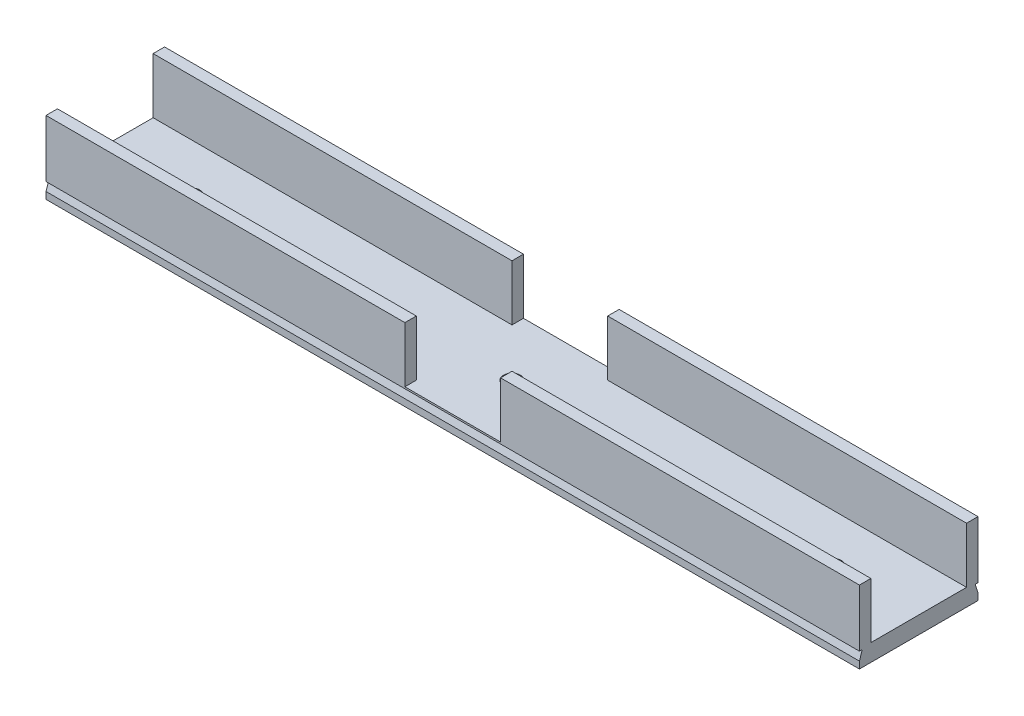
SolidWorks part; units mm, degrees
ref_plane "Front Plane" through (0, 0, 0) normal (0, 0, 1) x (1, 0, 0)
ref_plane "Top Plane" through (0, 0, 0) normal (0, 1, 0) x (1, 0, 0)
ref_plane "Right Plane" through (0, 0, 0) normal (1, 0, 0) x (0, 0, -1)
sketch "Croquis1" plane through (0, 0, 0) normal (0, 1, 0) x (1, 0, 0)
  line L0 (-71, -12.5) -> (-71, 12.5)
  line L1 (-71, -12.5) -> (71, -12.5)
  line L2 (-71, 12.5) -> (71, 12.5)
  line L3 (71, -12.5) -> (71, 12.5)
  line L4 (-71, -12.5) -> (71, 12.5) construction
  line L5 (-71, 12.5) -> (71, -12.5) construction
  line L6 (71, -10.35) -> (71, 10.35)
  line L7 (71, -10.35) -> (-71, -10.35)
  line L8 (71, 10.35) -> (-71, 10.35)
  line L9 (-71, -10.35) -> (-71, 10.35)
  line L10 (71, -10.35) -> (-71, 10.35) construction
  line L11 (71, 10.35) -> (-71, -10.35) construction
  point P1 (0, 0)
  point P2 (0, 0)
  dimension "D1" = 142
  dimension "D2" = 25
  dimension "D3" = 142
  dimension "D4" = 2.15
extrude "Saliente-Extruir2" add sketch "Croquis1" along normal blind 3 contours L3 L8 L0 L7
sketch "Croquis6" plane through (0, 3, 0) normal (0, 1, 0) x (1, 0, 0)
  line L0 (0, 0) -> (0, 6.8298) construction
  line L1 (-71, -10.35) -> (-71, 10.35) construction
  circle A0 centre (-56, 0) radius 1.5
  circle A1 centre (0, 0) radius 1.5
  circle A2 centre (56, 0) radius 1.5
  point P9 (-71, 0)
  dimension "D1" = 3
  dimension "D2" = 3
  dimension "D3" = 15
extrude "Cortar-Extruir4" cut sketch "Croquis6" against normal blind 3
sketch "Croquis7" plane through (0, 3, 0) normal (0, 1, 0) x (1, 0, 0)
  line L0 (-71, 8.35) -> (-71, 10.35)
  line L1 (-71, -10.35) -> (-71, 10.35) construction
  line L2 (-71, 10.35) -> (71, 10.35)
  line L3 (71, -10.35) -> (71, 10.35) construction
  line L4 (71, 10.35) -> (-71, 10.35) construction
  line L5 (71, 10.35) -> (71, 8.35)
  line L6 (71, 8.35) -> (-71, 8.35)
  line L7 (0, 0) -> (-103.6833, 0) construction
  line L8 (71, -8.35) -> (-71, -8.35)
  line L9 (71, -10.35) -> (71, -8.35)
  line L10 (-71, -10.35) -> (71, -10.35)
  line L11 (-71, -8.35) -> (-71, -10.35)
  dimension "D1" = 2
extrude "Saliente-Extruir3" add sketch "Croquis7" along normal blind 9.7
sketch "Croquis9" plane through (-71, 0, 0) normal (-1, 0, 0) x (0, 0, 1)
  line L1 (-10.35, 2.7) -> (-9.85, 2.7)
  line L2 (-10.35, 12.7) -> (-10.35, 0) construction
  line L3 (-9.85, 2.7) -> (-10.35, 1.2)
  line L4 (-10.35, 1.2) -> (-10.35, 2.7)
  line L5 (-10.35, 12.7) -> (-8.35, 12.7) construction
  line L6 (0, 0) -> (0, 4.8094) construction
  line L7 (10.35, 0) -> (-10.35, 0) construction
  line L8 (10.35, 2.7) -> (9.85, 2.7)
  line L9 (10.35, 1.2) -> (10.35, 2.7)
  line L10 (9.85, 2.7) -> (10.35, 1.2)
  dimension "D1" = 10
  dimension "D2" = 1.5
  dimension "D3" = 0.5
extrude "Cortar-Extruir5" cut sketch "Croquis9" against normal blind 224
sketch "Croquis10" plane through (0, 0, 10.35) normal (0, 0, 1) x (1, 0, 0)
  line L0 (-8.35, 3) -> (8.35, 3)
  line L1 (-8.35, 3) -> (-8.35, 12.7)
  line L2 (8.35, 3) -> (8.35, 12.7)
  line L3 (-8.35, 12.7) -> (8.35, 12.7)
  line L4 (-8.35, 3) -> (8.35, 12.7) construction
  line L5 (8.35, 3) -> (-8.35, 12.7) construction
  line L6 (71, 0) -> (-71, 0) construction
  point P1 (0, 7.85)
  point P3 (0, 0)
  point P8 (0, 0)
  dimension "D1" = 3
  dimension "D2" = 9.7
  dimension "D3" = 16.7
extrude "Cortar-Extruir6" cut sketch "Croquis10" against normal blind 80
